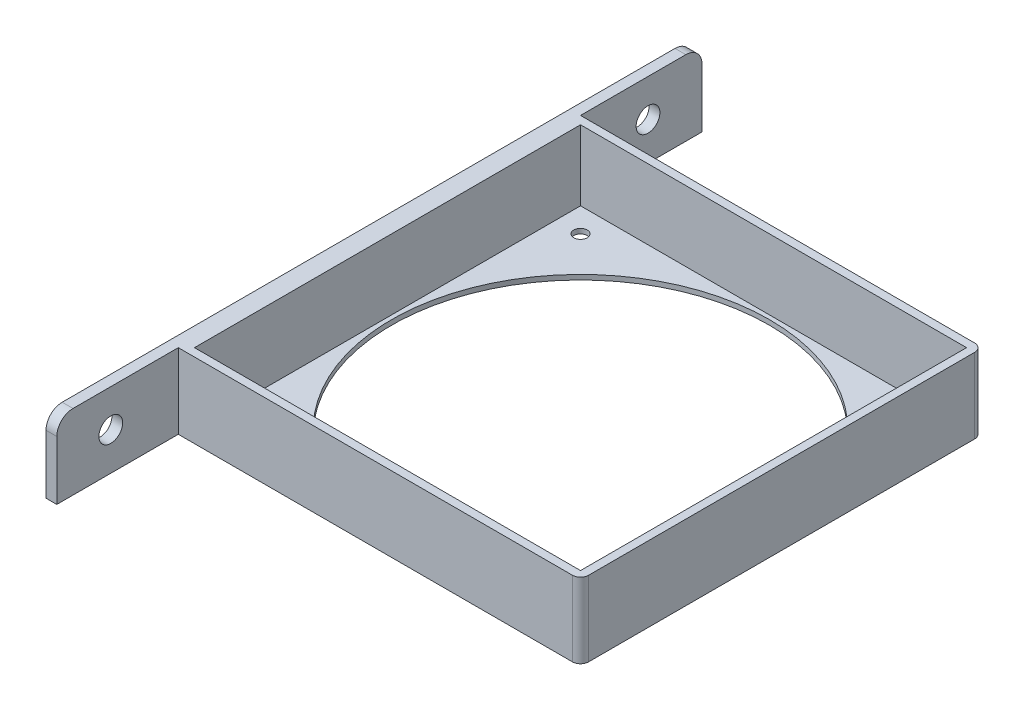
SolidWorks part; units mm, degrees
ref_plane "Front Plane" through (0, 0, 0) normal (0, 0, 1) x (1, 0, 0)
ref_plane "Top Plane" through (0, 0, 0) normal (0, 1, 0) x (1, 0, 0)
ref_plane "Right Plane" through (0, 0, 0) normal (1, 0, 0) x (0, 0, -1)
sketch "Sketch1" plane through (0, 0, 0) normal (0, 1, 0) x (1, 0, 0)
  line L0 (-71.5, 71.5) -> (71.5, 71.5)
  line L4 (74.5, 71.5) -> (74.5, -71.5)
  line L5 (-74.5, 74.5) -> (74.5, -74.5) construction
  line L6 (-74.5, -74.5) -> (74.5, 74.5) construction
  line L7 (71.5, 71.5) -> (71.5, -71.5)
  line L8 (-71.5, -71.5) -> (71.5, -71.5)
  line L9 (-71.5, 71.5) -> (-71.5, -71.5)
  line L10 (71.5, -74.5) -> (-74.5, -74.5)
  line L11 (-74.5, -74.5) -> (-74.5, 74.5)
  line L12 (-74.5, 74.5) -> (71.5, 74.5)
  line L14 (-71.5, -74.5) -> (71.5, -74.5) construction
  line L15 (-74.5, 71.5) -> (-74.5, -71.5) construction
  line L16 (-71.5, 74.5) -> (71.5, 74.5) construction
  arc A1 (71.5, -74.5) -> (74.5, -71.5) centre (71.5, -71.5) ccw
  arc A2 (74.5, 71.5) -> (71.5, 74.5) centre (71.5, 71.5) ccw
  arc A4 (71.5, 71.5) -> (71.5, 71.5) centre (71.5, 71.5) ccw
  arc A5 (71.5, -71.5) -> (71.5, -71.5) centre (71.5, -71.5) ccw
  arc A6 (-71.5, -71.5) -> (-71.5, -71.5) centre (-71.5, -71.5) cw
  arc A7 (-71.5, 71.5) -> (-71.5, 71.5) centre (-71.5, 71.5) ccw
  arc A8 (-71.5, 74.5) -> (-74.5, 71.5) centre (-71.5, 71.5) ccw construction
  arc A9 (-71.5, -74.5) -> (-74.5, -71.5) centre (-71.5, -71.5) cw construction
  point P0 (0, 0)
  dimension "D1" = 149
  dimension "D2" = 149
  dimension "D4" = 3
extrude "Boss-Extrude1" add sketch "Sketch1" along normal blind 26
sketch "Sketch2" plane through (0, 0, 0) normal (0, -1, 0) x (1, 0, 0)
  line L0 (0, 74.5) -> (0, -74.5) construction
  line L4 (74.5, -71.5) -> (74.5, 71.5)
  line L5 (-74.5, -74.5) -> (74.5, 74.5) construction
  line L6 (-74.5, 74.5) -> (74.5, -74.5) construction
  line L7 (-74.5, 0) -> (74.5, 0) construction
  line L8 (71.5, 74.5) -> (-74.5, 74.5)
  line L9 (-74.5, 74.5) -> (-74.5, -74.5)
  line L10 (-74.5, -74.5) -> (71.5, -74.5)
  arc A1 (71.5, -74.5) -> (74.5, -71.5) centre (71.5, -71.5) ccw
  arc A2 (74.5, 71.5) -> (71.5, 74.5) centre (71.5, 71.5) ccw
  circle A4 centre (0, 0) radius 70
  circle A5 centre (-62.5, 62.5) radius 2.5
  circle A6 centre (62.5, 62.5) radius 2.5
  circle A7 centre (62.5, -62.5) radius 2.5
  circle A8 centre (-62.5, -62.5) radius 2.5
  point P0 (0, 0)
  point P35 (0, 0)
  dimension "D2" = 62.5
  dimension "D3" = 62.5
  dimension "D4" = 4
extrude "Boss-Extrude2" add sketch "Sketch2" along normal blind 1.8
sketch "Sketch3" plane through (-74.5, 0, 0) normal (-1, 0, 0) x (0, 0, 1)
  line L0 (74.5, 26) -> (74.5, -1.8) construction
  line L1 (-113.5, 26) -> (113.5, 26)
  line L2 (-119.5, 20) -> (-119.5, -1.8)
  line L3 (-119.5, -1.8) -> (119.5, -1.8)
  line L4 (119.5, 20) -> (119.5, -1.8)
  line L5 (-119.5, 26) -> (119.5, -1.8) construction
  line L6 (-119.5, -1.8) -> (119.5, 26) construction
  arc A0 (-113.5, 26) -> (-119.5, 20) centre (-113.5, 20) ccw
  arc A1 (113.5, 26) -> (119.5, 20) centre (113.5, 20) cw
  circle A2 centre (-99.5, 12.2) radius 4.4
  circle A3 centre (99.5, 12.2) radius 4.4
  point P0 (0, 12.1)
  dimension "D3" = 6
  dimension "D4" = 6
  dimension "D5" = 20
  dimension "D1" = 239
  dimension "D2" = 45
  dimension "D6" = 14
  dimension "D7" = 20
  dimension "D8" = 14
extrude "Boss-Extrude4" add sketch "Sketch3" along normal blind 4
